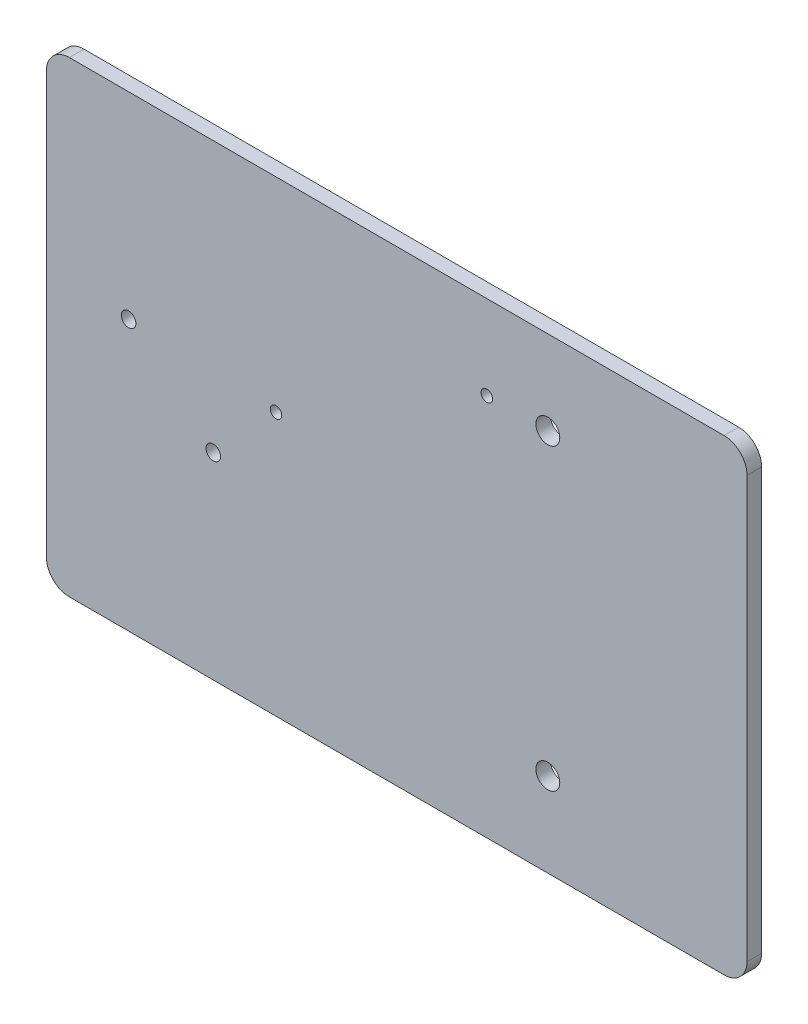
SolidWorks part; units mm, degrees
ref_plane "Front Plane" through (0, 0, 0) normal (0, 0, 1) x (1, 0, 0)
ref_plane "Top Plane" through (0, 0, 0) normal (0, 1, 0) x (1, 0, 0)
ref_plane "Right Plane" through (0, 0, 0) normal (1, 0, 0) x (0, 0, -1)
sketch "Sketch1" plane through (0, 0, 0) normal (0, 0, 1) x (1, 0, 0)
  line L1 (0, 0) -> (152.4, 0)
  line L2 (0, 0) -> (0, 101.6)
  line L3 (0, 101.6) -> (152.4, 101.6)
  line L4 (152.4, 0) -> (152.4, 101.6)
  dimension "D1" = 152.4
  dimension "D2" = 101.6
extrude "Boss-Extrude1" add sketch "Sketch1" along normal blind 3.175
sketch "Sketch2" plane through (0, 0, 3.175) normal (0, 0, 1) x (1, 0, 0)
  line L0 (17.8793, 58.74) -> (36.2993, 42.86) construction
  line L1 (109.0683, 83.3) -> (109.0683, 18.3) construction
  line L2 (152.4, 0) -> (152.4, 101.6) construction
  line L3 (152.4, 50.8) -> (0, 50.8) construction
  line L4 (0, 101.6) -> (0, 0) construction
  circle A0 centre (109.0683, 18.3) radius 2.6
  circle A1 centre (109.0683, 83.3) radius 2.6
  circle A2 centre (95.7972, 83.3) radius 1.25
  circle A3 centre (49.9472, 57.26) radius 1.25
  circle A4 centre (17.8793, 58.74) radius 1.5875
  circle A5 centre (36.2993, 42.86) radius 1.5875
  point P6 (109.0683, 50.8)
  point P17 (27.0893, 50.8)
  dimension "D1" = 2
  dimension "D2" = 45.85
  dimension "D4" = 18.42
  dimension "D3" = 26.04
  dimension "D5" = 15.88
extrude "Cut-Extrude1" cut sketch "Sketch2" against normal up to next
fillet "Fillet1" radius 5 4 edges at (0, 101.6, 1.5875) (0, 0, 1.5875) (152.4, 0, 1.5875) (152.4, 101.6, 1.5875)
